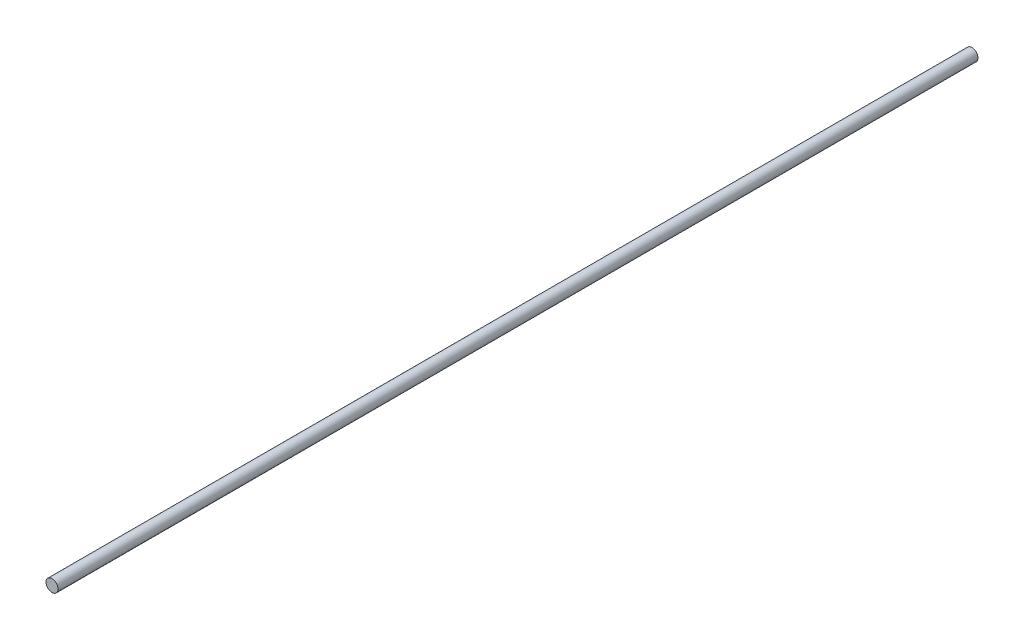
SolidWorks part; units mm, degrees
ref_plane "Front Plane" through (0, 0, 0) normal (0, 0, 1) x (1, 0, 0)
ref_plane "Top Plane" through (0, 0, 0) normal (0, 1, 0) x (1, 0, 0)
ref_plane "Right Plane" through (0, 0, 0) normal (1, 0, 0) x (0, 0, -1)
sketch "Croquis1" plane through (0, 0, 0) normal (0, 0, 1) x (1, 0, 0)
  circle A0 centre (0, 0) radius 3.5
  dimension "D1" = 7
extrude "Saliente-Extruir1" add sketch "Croquis1" along normal blind 535
